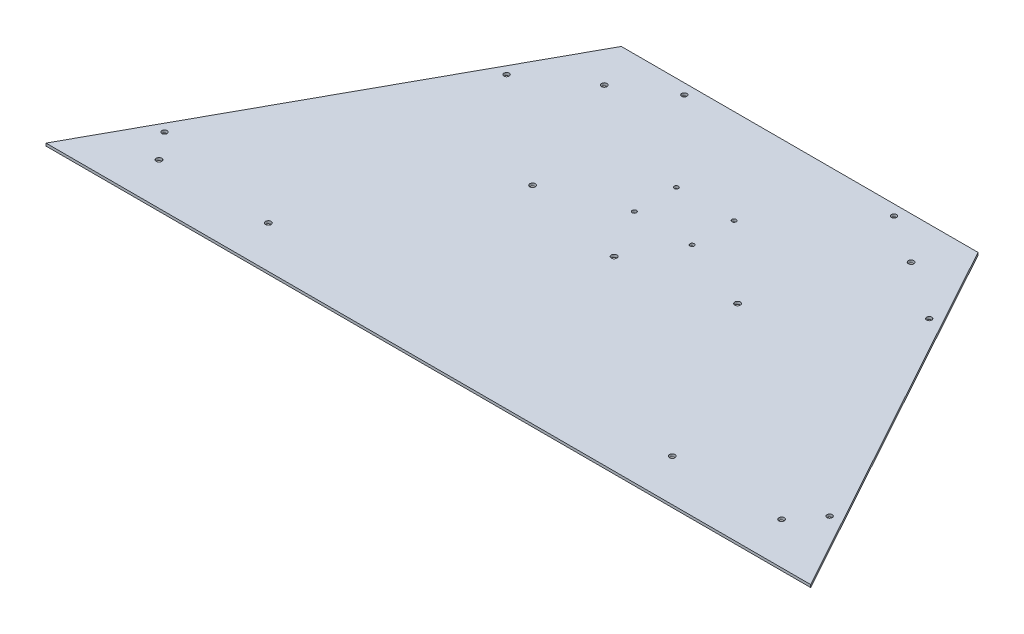
SolidWorks part; units mm, degrees
material "PC High Viscosity"
ref_plane "Front Plane" through (0, 0, 0) normal (0, 0, 1) x (1, 0, 0)
ref_plane "Top Plane" through (0, 0, 0) normal (0, 1, 0) x (1, 0, 0)
ref_plane "Right Plane" through (0, 0, 0) normal (1, 0, 0) x (0, 0, -1)
sketch "Sketch1" plane through (0, 0, 0) normal (0, 1, 0) x (1, 0, 0)
  line L0 (-462.534, 0) -> (-215.773, 449.265)
  line L1 (-215.773, 449.265) -> (215.773, 449.265)
  line L2 (215.773, 449.265) -> (462.534, 0)
  line L3 (462.534, 0) -> (-462.534, 0)
  point P2 (0, 0)
  dimension "D1" = 925.068
  dimension "D2" = 512.572
  dimension "D3" = 431.546
extrude "Boss-Extrude1" add sketch "Sketch1" along normal blind 3.175
hole_wizard "1/4 (0.25) Diameter Hole1" positions "Sketch2" profile "Sketch3" hole size "1/4" standard "ANSI Inch" end condition through all
sketch "Sketch2" plane through (0, 3.175, 0) normal (0, 1, 0) x (1, 0, 0)
  line L0 (0, 0) -> (0, 449.265) construction
  line L1 (215.773, 449.265) -> (-215.773, 449.265) construction
  line L3 (-402.3683, 83.1602) -> (-413.4997, 89.2742) construction
  line L4 (-215.773, 449.265) -> (-462.534, 0) construction
  line L6 (-255.6323, 350.3148) -> (-266.7638, 356.4288) construction
  line L8 (-126.873, 436.565) -> (-126.873, 449.265) construction
  point P0 (-402.3683, 83.1602)
  point P2 (-255.6323, 350.3148)
  point P4 (-126.873, 436.565)
  point P33 (402.3683, 83.1602)
  point P34 (255.6323, 350.3148)
  point P35 (126.873, 436.565)
  dimension "D1" = 101.854
  dimension "D2" = 406.654
  dimension "D3" = 12.7
  dimension "D4" = 88.9
sketch "Sketch3" plane through (-402.3683, 3.175, -83.1602) normal (1, 0, 0) x (0, 0, 1)
  line L0 (0, 0) -> (0, 3.175)
  line L1 (0, 3.175) -> (3.175, 3.175)
  line L2 (3.175, 3.175) -> (3.175, 0)
  line L5 (3.175, 0) -> (0, 0)
  line L11 (0, -6.35) -> (0, 107.95) construction
  dimension "Thru Hole Dia." = 6.35
  dimension "Thru Hole Depth" = 3.175
hole_wizard "1/4 Clearance Hole1" positions "Sketch4" profile "Sketch5" hole size "1/4" standard "ANSI Inch" end condition through all
sketch "Sketch4" plane through (0, 3.175, 0) normal (0, 1, 0) x (1, 0, 0)
  line L0 (0, 0) -> (0, 449.265) construction
  line L1 (215.773, 449.265) -> (-215.773, 449.265) construction
  line L3 (-462.534, 0) -> (462.534, 0) construction
  point P0 (-376.682, 50.8)
  point P2 (-244.348, 50.8)
  point P4 (-123.952, 250.19)
  point P6 (-185.674, 398.526)
  point P19 (0, 224.79)
  point P28 (376.682, 50.8)
  point P29 (244.348, 50.8)
  point P30 (185.674, 398.526)
  point P31 (123.952, 250.19)
  dimension "D1" = 50.8
  dimension "D2" = 244.348
  dimension "D3" = 376.682
  dimension "D4" = 123.952
  dimension "D5" = 250.19
  dimension "D6" = 185.674
  dimension "D7" = 398.526
  dimension "D8" = 224.79
sketch "Sketch5" plane through (-376.682, 3.175, -50.8) normal (1, 0, 0) x (0, 0, 1)
  line L0 (0, 0) -> (0, 3.175)
  line L1 (0, 3.175) -> (3.3782, 3.175)
  line L2 (3.3782, 3.175) -> (3.3782, 0)
  line L5 (3.3782, 0) -> (0, 0)
  line L11 (0, -6.35) -> (0, 107.95) construction
  dimension "Thru Hole Dia." = 6.7564
  dimension "Thru Hole Depth" = 3.175
hole_wizard "#7 (0.201) Diameter Hole1" positions "Sketch6" profile "Sketch7" hole size "#7" standard "ANSI Inch" end condition through all
sketch "Sketch6" plane through (0, 3.175, 0) normal (0, 1, 0) x (1, 0, 0)
  line L0 (-462.534, 0) -> (462.534, 0) construction
  line L8 (0, 0) -> (0, 449.265) construction
  line L9 (215.773, 449.265) -> (-215.773, 449.265) construction
  point P20 (0, 0)
  point P239 (-34.925, 334.965)
  point P241 (-34.925, 284.165)
  point P244 (0, 0)
  point P245 (34.925, 284.165)
  point P246 (34.925, 334.965)
  point P247 (0, 0)
  point P248 (-69.7716, 416.0741)
  point P249 (-44.45, 337.7694)
  point P250 (0, 0)
  dimension "D2" = 69.85
  dimension "D5" = 50.8
  dimension "D6" = 114.3
sketch "Sketch7" plane through (34.925, 3.175, -334.965) normal (1, 0, 0) x (0, 0, 1)
  line L0 (0, 0) -> (0, 3.175)
  line L1 (0, 3.175) -> (2.5527, 3.175)
  line L2 (2.5527, 3.175) -> (2.5527, 0)
  line L5 (2.5527, 0) -> (0, 0)
  line L11 (0, -6.35) -> (0, 107.95) construction
  dimension "Thru Hole Dia." = 5.1054
  dimension "Thru Hole Depth" = 3.175
